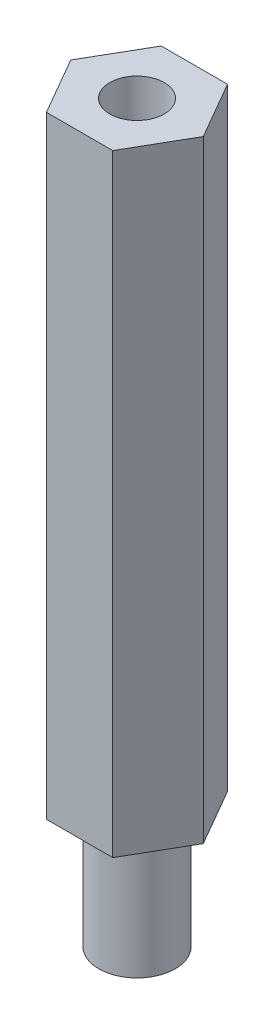
SolidWorks part; units mm, degrees
ref_plane "Front" through (0, 0, 0) normal (0, 0, 1) x (1, 0, 0)
ref_plane "Top" through (0, 0, 0) normal (0, 1, 0) x (1, 0, 0)
ref_plane "Right" through (0, 0, 0) normal (1, 0, 0) x (0, 0, -1)
sketch "Sketch1" plane through (0, 0, 0) normal (0, 1, 0) x (1, 0, 0)
  line L0 (-1.3748, 2.3812) -> (1.3748, 2.3812)
  line L1 (1.3748, 2.3812) -> (2.7496, 0)
  line L2 (2.7496, 0) -> (1.3748, -2.3813)
  line L3 (1.3748, -2.3813) -> (-1.3748, -2.3813)
  line L4 (-1.3748, -2.3813) -> (-2.7496, 0)
  line L5 (-2.7496, 0) -> (-1.3748, 2.3812)
  line L6 (0, 6.9504) -> (0, -7.1631) construction
  line L8 (-1.3748, 2.3812) -> (1.3748, -2.3813) construction
  line L9 (-1.3748, -2.3813) -> (1.3748, 2.3812) construction
  line L10 (-2.7496, 0) -> (2.7496, 0) construction
  point P0 (0, 0)
  point P1 (2.7496, 0)
  point P3 (1.3748, 2.3812)
  point P4 (-1.3748, 2.3812)
  point P5 (-2.7496, 0)
  point P6 (-1.3748, -2.3813)
  point P7 (1.3748, -2.3813)
  dimension "D1" = 4.7625
extrude "Extrude1" add sketch "Sketch1" along normal blind 25.4
hole_wizard "#4-40 Tapped Hole1" positions "3DSketch1" profile "Sketch2" tap size "#4-40" standard "Ansi Inch"
sketch3d "3DSketch1"
  line L0 (-1.3748, 25.4, -2.3812) -> (1.3748, 25.4, 2.3813) construction
  line L1 (-1.3748, 25.4, -2.3812) -> (-2.7496, 25.4, 0) construction
  line L2 (1.3748, 25.4, -2.3812) -> (-1.3748, 25.4, -2.3812) construction
  point P0 (0, 25.4, 0)
sketch "Sketch2" plane through (0, 25.4, 0) normal (1, 0, 0) x (0, 0, 1)
  line L0 (0, 0) -> (0, 8.2992)
  line L1 (0, 8.2992) -> (1.1303, 7.62)
  line L2 (1.1303, 7.62) -> (1.1303, 0)
  line L5 (1.1303, 0) -> (0, 0)
  line L10 (0, 8.2992) -> (-1.1303, 7.62) construction
  line L11 (0, -6.35) -> (0, 107.95) construction
  dimension "Tap Drill Dia." = 2.2606
  dimension "Tap Drill Depth" = 7.62
  dimension "Drill Angle" = 118
cosmetic thread "Hole Thread1" parameters "D1"=5.588, "D2"=2.8448
sketch "Sketch5" plane through (0, 0, 0) normal (0, -1, 0) x (1, 0, 0)
  circle A0 centre (0, 0) radius 1.5875
  dimension "D1" = 3.175
extrude "Extrude2" add sketch "Sketch5" along normal blind 5.08
cosmetic thread "Cosmetic Thread1" parameters "D2"=2.2606
